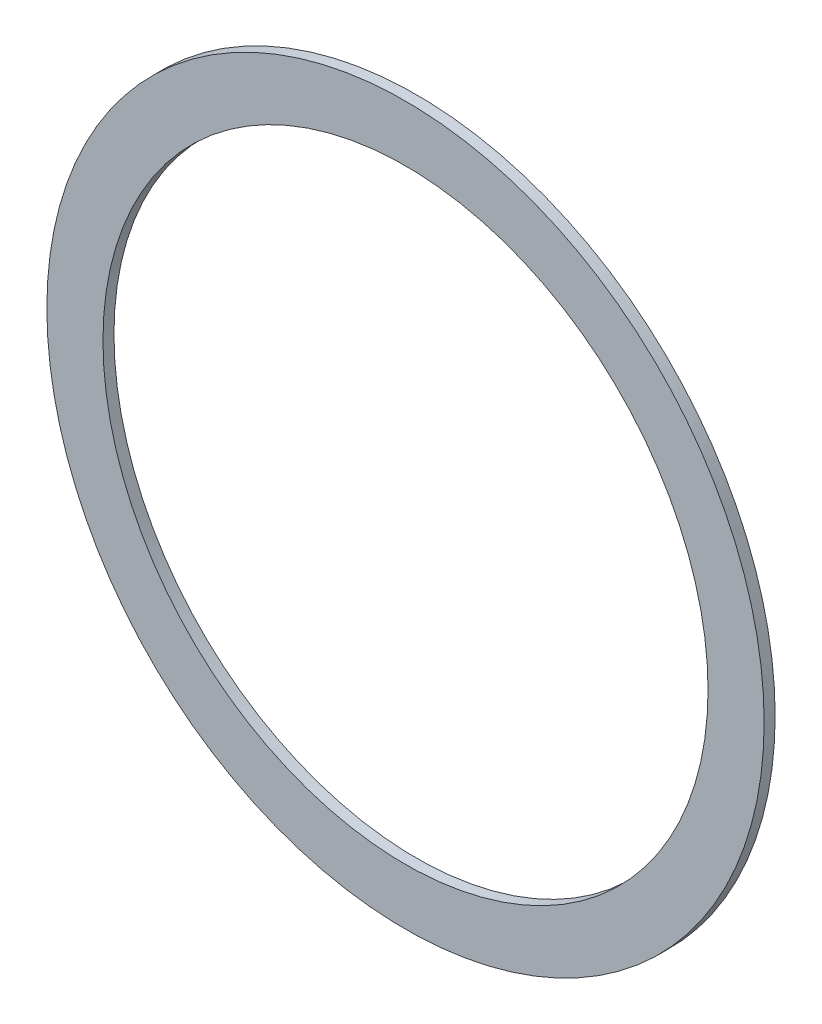
SolidWorks part; units mm, degrees
ref_plane "Front Plane" through (0, 0, 0) normal (0, 0, 1) x (1, 0, 0)
ref_plane "Top Plane" through (0, 0, 0) normal (0, 1, 0) x (1, 0, 0)
ref_plane "Right Plane" through (0, 0, 0) normal (1, 0, 0) x (0, 0, -1)
sketch "Sketch1" plane through (0, 0, 0) normal (0, 0, 1) x (1, 0, 0)
  circle A0 centre (0, 0) radius 2.75
  circle A1 centre (0, 0) radius 3.5866
  dimension "D1" = 5.5
extrude "Boss-Extrude1" add sketch "Sketch1" along normal blind 0.1
sketch "Sketch2" plane through (0, 0, 0.1) normal (0, 0, 1) x (1, 0, 0)
  circle A0 centre (0, 0) radius 3.26
  circle A1 centre (0, 0) radius 4.1442
  dimension "D1" = 6.52
extrude "Cut-Extrude1" cut sketch "Sketch2" against normal blind 10
